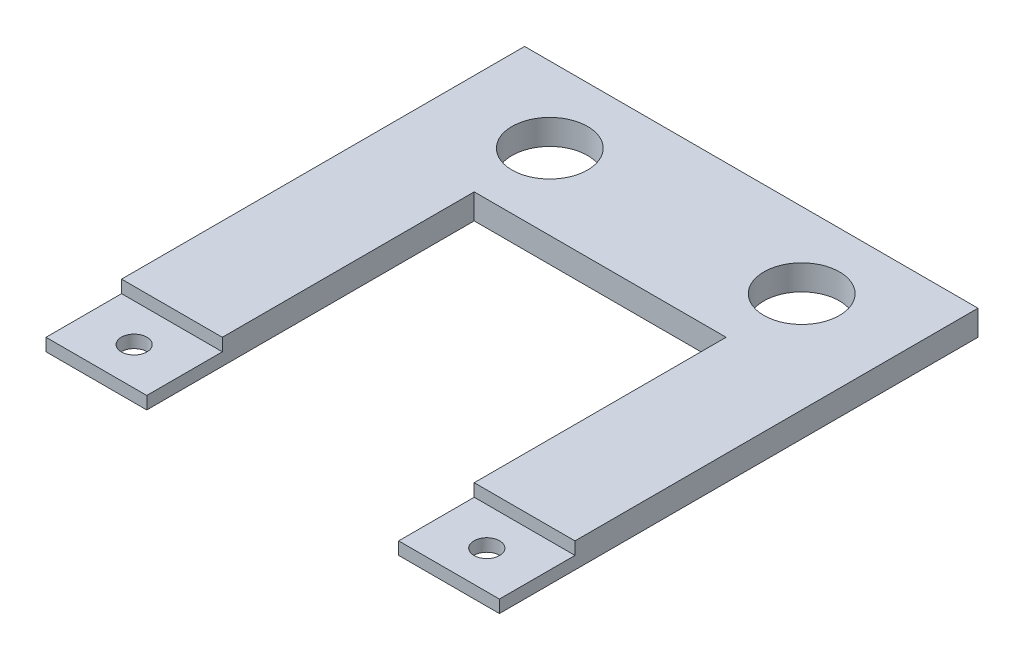
SolidWorks part; units mm, degrees
ref_plane "Front Plane" through (0, 0, 0) normal (0, 0, 1) x (1, 0, 0)
ref_plane "Top Plane" through (0, 0, 0) normal (0, 1, 0) x (1, 0, 0)
ref_plane "Right Plane" through (0, 0, 0) normal (1, 0, 0) x (0, 0, -1)
sketch "Sketch1" plane through (0, 0, 0) normal (0, 1, 0) x (1, 0, 0)
  line L1 (-14.2875, 15.0812) -> (14.2875, 15.0812)
  line L2 (-14.2875, 15.0812) -> (-14.2875, -15.0813)
  line L3 (-14.2875, -15.0813) -> (14.2875, -15.0812)
  line L4 (14.2875, 15.0812) -> (14.2875, -15.0812)
  line L5 (-7.9375, -15.0813) -> (7.9375, -15.0813)
  line L6 (-7.9375, -15.0813) -> (-7.9375, 5.5563)
  line L7 (-7.9375, 5.5563) -> (7.9375, 5.5563)
  line L8 (7.9375, -15.0813) -> (7.9375, 5.5563)
  point P4 (0, 15.0813)
  point P6 (-14.2875, 0)
  point P11 (0, 5.5563)
  dimension "D1" = 28.575
  dimension "D2" = 30.1625
  dimension "D3" = 6.35
  dimension "D4" = 9.525
extrude "Boss-Extrude1" add sketch "Sketch1" along normal mid plane 1.5875 contours L8 L3 L4 L1 L2 L6 L7
sketch "Sketch2" plane through (0, 0.7937, 0) normal (0, 1, 0) x (1, 0, 0)
  line L0 (-7.9375, -15.0813) -> (-7.9375, 5.5563) construction
  line L1 (-14.2875, -15.0813) -> (-7.9375, -15.0813)
  line L2 (-14.2875, -15.0813) -> (-14.2875, -10.3188)
  line L3 (-14.2875, -10.3188) -> (-7.9375, -10.3188)
  line L4 (-7.9375, -15.0813) -> (-7.9375, -10.3188)
  line L5 (14.2875, 15.0812) -> (14.2875, -15.0812) construction
  line L6 (7.9375, -15.0812) -> (14.2875, -15.0812)
  line L7 (7.9375, -15.0812) -> (7.9375, -10.3188)
  line L8 (7.9375, -10.3188) -> (14.2875, -10.3188)
  line L9 (14.2875, -15.0812) -> (14.2875, -10.3188)
  dimension "D1" = 4.7625
extrude "Cut-Extrude1" cut sketch "Sketch2" against normal blind 0.7937
sketch "Sketch3" plane through (0, 0.7937, 0) normal (0, 1, 0) x (1, 0, 0)
  line L0 (-7.9375, -10.3188) -> (-14.2875, -10.3188) construction
  line L1 (-14.2875, -10.3188) -> (-14.2875, -15.0813) construction
  line L2 (0, -1000) -> (0, 49000) construction
  line L3 (-14.2875, 15.0812) -> (-14.2875, -10.3188) construction
  line L4 (-14.2875, 15.0812) -> (14.2875, 15.0812) construction
  circle A0 centre (-11.1125, -12.7) radius 0.8065
  circle A1 centre (-7.9375, 10.3187) radius 2.3813
  circle A2 centre (11.1125, -12.7) radius 0.8065
  circle A3 centre (7.9375, 10.3187) radius 2.3813
  point P6 (-11.1125, -10.3188)
  point P9 (-14.2875, -12.7)
  dimension "D1" = 1.6129
  dimension "D2" = 4.7625
  dimension "D3" = 6.35
  dimension "D4" = 4.7625
extrude "Cut-Extrude2" cut sketch "Sketch3" against normal up to surface (1.5875 mm away) from surface at 0 up to face at (0, -0.7937, 2.3812) starting at face at (0, 0.7937, 0)
